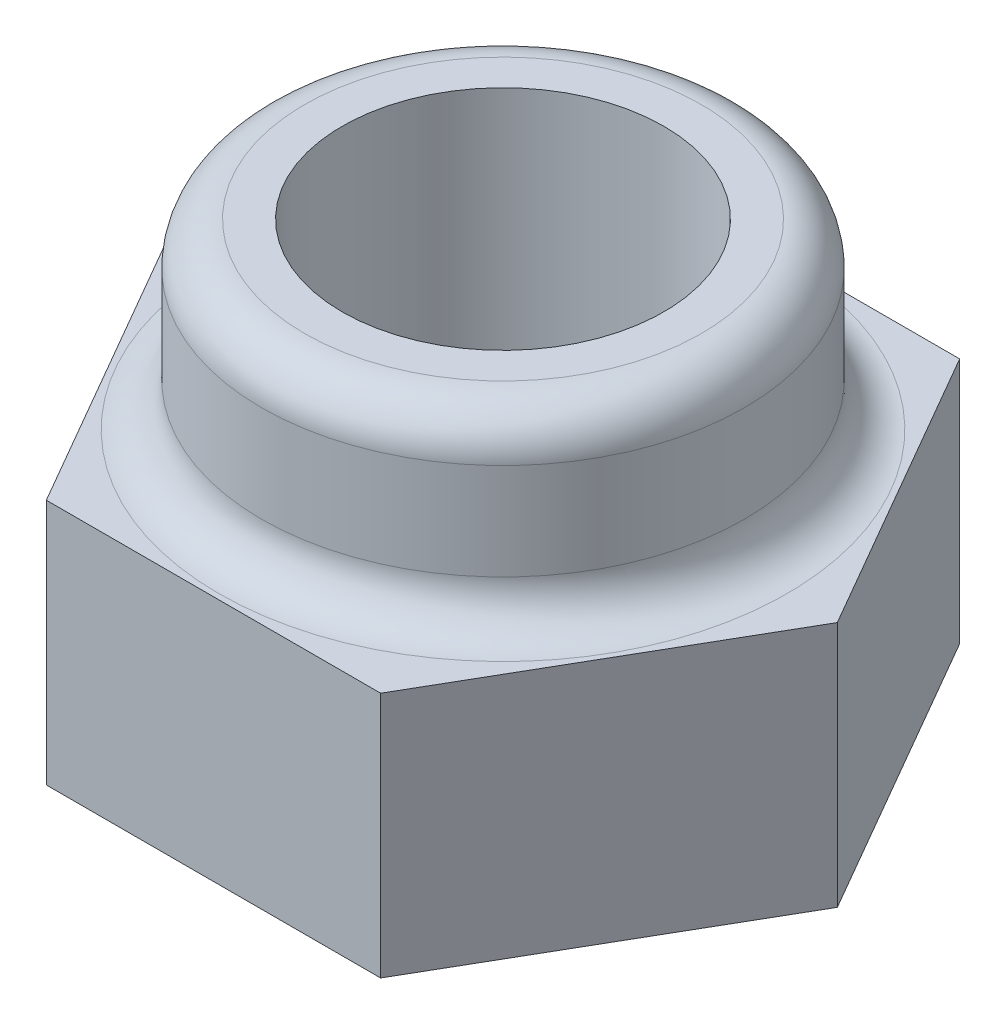
SolidWorks part; units mm, degrees
ref_plane "前视基准面" through (0, 0, 0) normal (0, 0, 1) x (1, 0, 0)
ref_plane "上视基准面" through (0, 0, 0) normal (0, 1, 0) x (1, 0, 0)
ref_plane "右视基准面" through (0, 0, 0) normal (1, 0, 0) x (0, 0, -1)
sketch "草图1" plane through (0, 0, 0) normal (0, 1, 0) x (1, 0, 0)
  line L1 (3.1177, 0) -> (1.5588, 2.7)
  line L2 (1.5588, 2.7) -> (-1.5588, 2.7)
  line L3 (-1.5588, 2.7) -> (-3.1177, 0)
  line L4 (-3.1177, 0) -> (-1.5588, -2.7)
  line L5 (-1.5588, -2.7) -> (1.5588, -2.7)
  line L6 (1.5588, -2.7) -> (3.1177, 0)
  circle A0 centre (0, 0) radius 2.7 construction
  circle A1 centre (0, 0) radius 1.5
extrude "凸台-拉伸1" add sketch "草图1" along normal blind 2.3
sketch "草图2" plane through (0, 2.3, 0) normal (0, 1, 0) x (1, 0, 0)
  circle A0 centre (0, 0) radius 1.5
  circle A1 centre (0, 0) radius 2.25
extrude "凸台-拉伸2" add sketch "草图2" along normal blind 1.7
fillet "圆角1" radius 0.4 2 edges at (0, 2.3, 2.25) (0, 4, 2.25)
